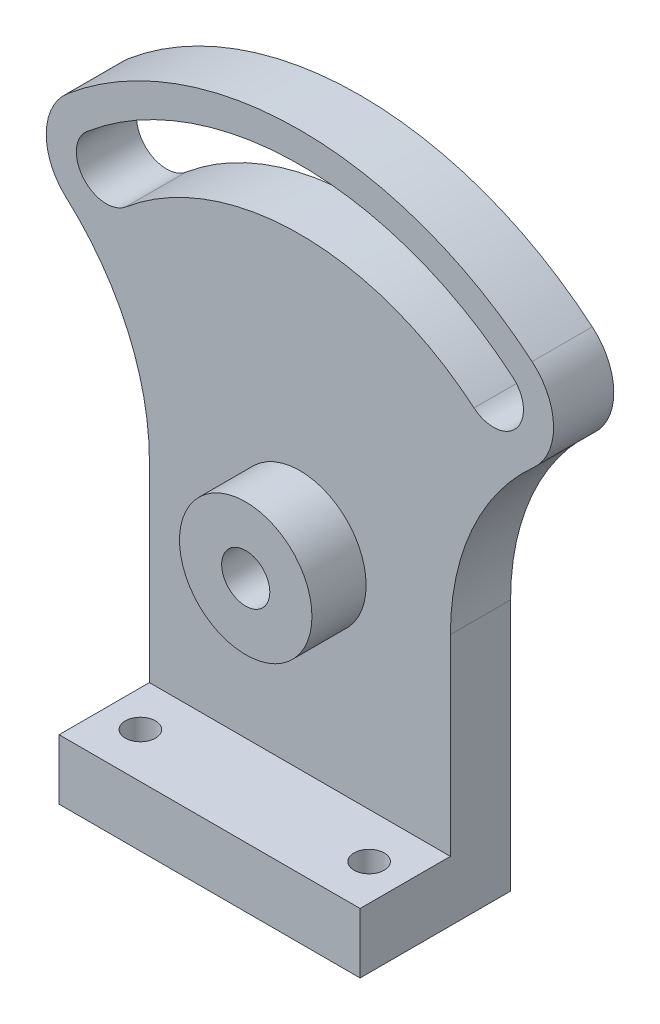
SolidWorks part; units mm, degrees
ref_plane "Front Plane" through (0, 0, 0) normal (0, 0, 1) x (1, 0, 0)
ref_plane "Top Plane" through (0, 0, 0) normal (0, 1, 0) x (1, 0, 0)
ref_plane "Right Plane" through (0, 0, 0) normal (1, 0, 0) x (0, 0, -1)
sketch "Sketch1" plane through (0, 0, 0) normal (0, 0, 1) x (1, 0, 0)
  line L0 (25, 0) -> (25, 41.9032)
  line L1 (-25, 0) -> (25, 0)
  line L2 (0, 0) -> (0, 102) construction
  line L3 (0, 42) -> (2.5712, 45.0642) construction
  line L4 (38.5673, 87.9627) -> (57.7398, 110.8116) construction
  line L7 (0, 42) -> (-2.5712, 45.0642) construction
  line L8 (-25, 0) -> (-25, 41.9032)
  arc A0 (28.9254, 76.472) -> (-28.9254, 76.472) centre (0, 42) ccw
  circle A1 centre (0, 42) radius 4
  arc A2 (38.5673, 87.9627) -> (-38.5673, 87.9627) centre (0, 42) ccw
  arc A3 (28.9254, 76.472) -> (35.3533, 84.1324) centre (32.1394, 80.3022) ccw
  arc A5 (35.3533, 84.1324) -> (-35.3533, 84.1324) centre (0, 42) ccw
  arc A6 (-38.8168, 72.8583) -> (-38.5673, 87.9627) centre (-32.1394, 80.3022) cw
  arc A7 (25, 41.9032) -> (38.8168, 72.8583) centre (66.5842, 41.9032) cw
  arc A8 (38.8168, 72.8583) -> (38.5673, 87.9627) centre (32.1394, 80.3022) ccw
  arc A9 (-25, 41.9032) -> (-38.8168, 72.8583) centre (-66.5842, 41.9032) ccw
  arc A11 (-28.9254, 76.472) -> (-35.3533, 84.1324) centre (-32.1394, 80.3022) cw
  point P8 (32.1394, 80.3022)
  dimension "D2" = 40
  dimension "D3" = 8
  dimension "D5" = 120
  dimension "D6" = 45
  dimension "D7" = 10
  dimension "D8" = 41.5842
  dimension "D1" = 42
  dimension "D4" = 25
extrude "Boss-Extrude1" add sketch "Sketch1" along normal blind 10
sketch "Sketch2" plane through (0, 0, 10) normal (0, 0, 1) x (1, 0, 0)
  line L0 (25, 0) -> (25, 41.9032) construction
  line L1 (-25, 0) -> (25, 0)
  line L2 (-25, 0) -> (-25, 10)
  line L3 (-25, 10) -> (25, 10)
  line L4 (25, 0) -> (25, 10)
  dimension "D1" = 10
extrude "Boss-Extrude2" add sketch "Sketch2" along normal blind 15
sketch "Sketch3" plane through (0, 10, 0) normal (0, 1, 0) x (1, 0, 0)
  line L0 (0, -25) -> (0, -10) construction
  line L1 (25, -25) -> (-25, -25) construction
  line L2 (-38.5673, -10) -> (38.5673, -10) construction
  line L3 (-19, -17.5) -> (19, -17.5)
  circle A0 centre (-19, -17.5) radius 2.5
  circle A1 centre (19, -17.5) radius 2.5
  point P8 (0, -17.5)
  point P9 (0, -17.5)
  dimension "D1" = 5
  dimension "D2" = 5
  dimension "D3" = 38
extrude "Cut-Extrude1" cut sketch "Sketch3" against normal through all
sketch "Sketch4" plane through (0, 0, 10) normal (0, 0, 1) x (1, 0, 0)
  circle A0 centre (0, 42) radius 11
  circle A1 centre (0, 42) radius 4
  dimension "D1" = 22
  dimension "D2" = 8
extrude "Boss-Extrude3" add sketch "Sketch4" along normal blind 9
